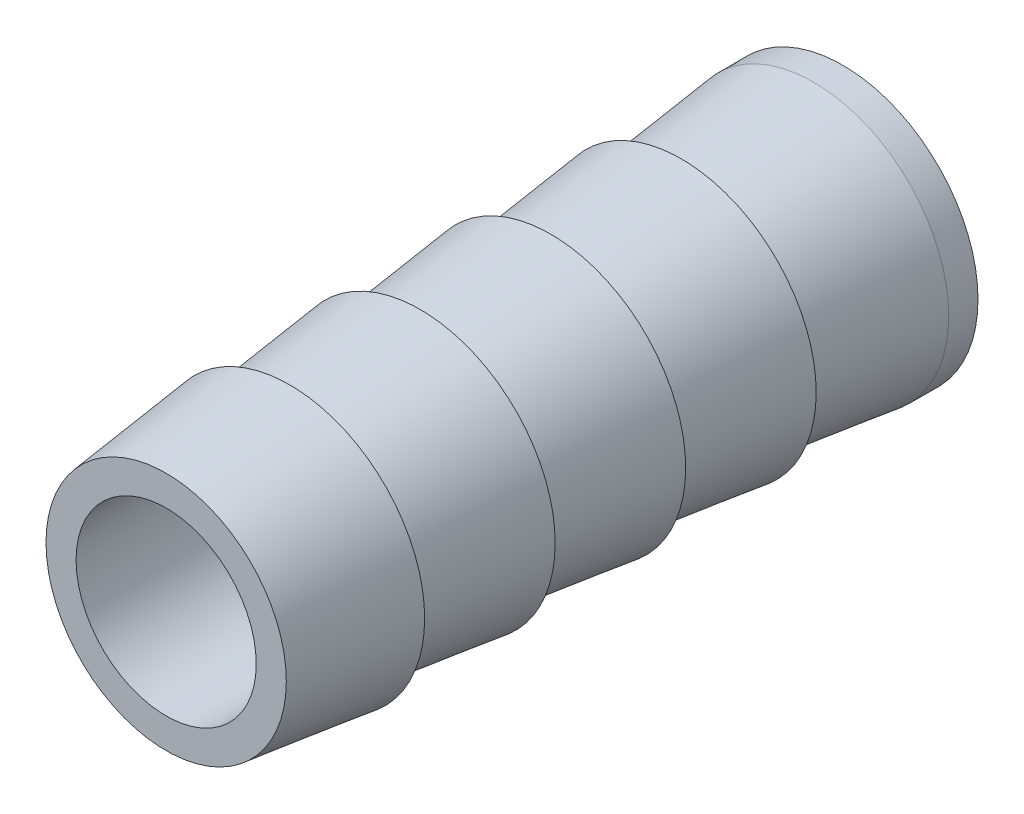
SolidWorks part; units mm, degrees
ref_plane "Front Plane" through (0, 0, 0) normal (0, 0, 1) x (1, 0, 0)
ref_plane "Top Plane" through (0, 0, 0) normal (0, 1, 0) x (1, 0, 0)
ref_plane "Right Plane" through (0, 0, 0) normal (1, 0, 0) x (0, 0, -1)
sketch "Sketch2" plane through (0, 0, 0) normal (1, 0, 0) x (0, 0, -1)
  line L0 (-15.2797, 0) -> (15.2797, 0) construction
  line L3 (-15.1117, 0) -> (-15.1117, 4.2348)
  line L5 (-15.1117, 4.2348) -> (-10.7545, 4.7536)
  line L6 (-10.7545, 4.7536) -> (-10.7545, 4.2059)
  line L8 (-15.1117, 0) -> (8.7392, 0)
  line L10 (-10.6053, 4.2237) -> (-6.1547, 4.7536)
  line L11 (-6.1547, 4.7536) -> (-6.1547, 4.2059)
  line L15 (-6.0056, 4.2237) -> (-1.5549, 4.7536)
  line L16 (-1.5549, 4.7536) -> (-1.5549, 4.2059)
  line L20 (-1.4058, 4.2237) -> (3.0449, 4.7536)
  line L23 (3.0449, 4.7536) -> (3.0449, 4.2059)
  line L24 (3.194, 4.2237) -> (7.708, 4.7612)
  line L27 (7.708, 4.7612) -> (8.7392, 4.7625)
  line L29 (-10.6053, 4.2237) -> (-10.7545, 4.2059)
  line L30 (-6.0056, 4.2237) -> (-6.1547, 4.2059)
  line L31 (-1.4058, 4.2237) -> (-1.5549, 4.2059)
  line L32 (3.194, 4.2237) -> (3.0449, 4.2059)
  line L33 (8.7392, 4.7625) -> (8.7392, 0)
revolve "Barbfitting(Mcmaster)" add sketch "Sketch2" angle 360 about L0
sketch "Sketch3" plane through (0, 0, 15.1117) normal (0, 0, 1) x (1, 0, 0)
  circle A0 centre (0, 0) radius 3.175
  dimension "D1" = 6.35
extrude "Cut-Extrude1" cut sketch "Sketch3" against normal through all
